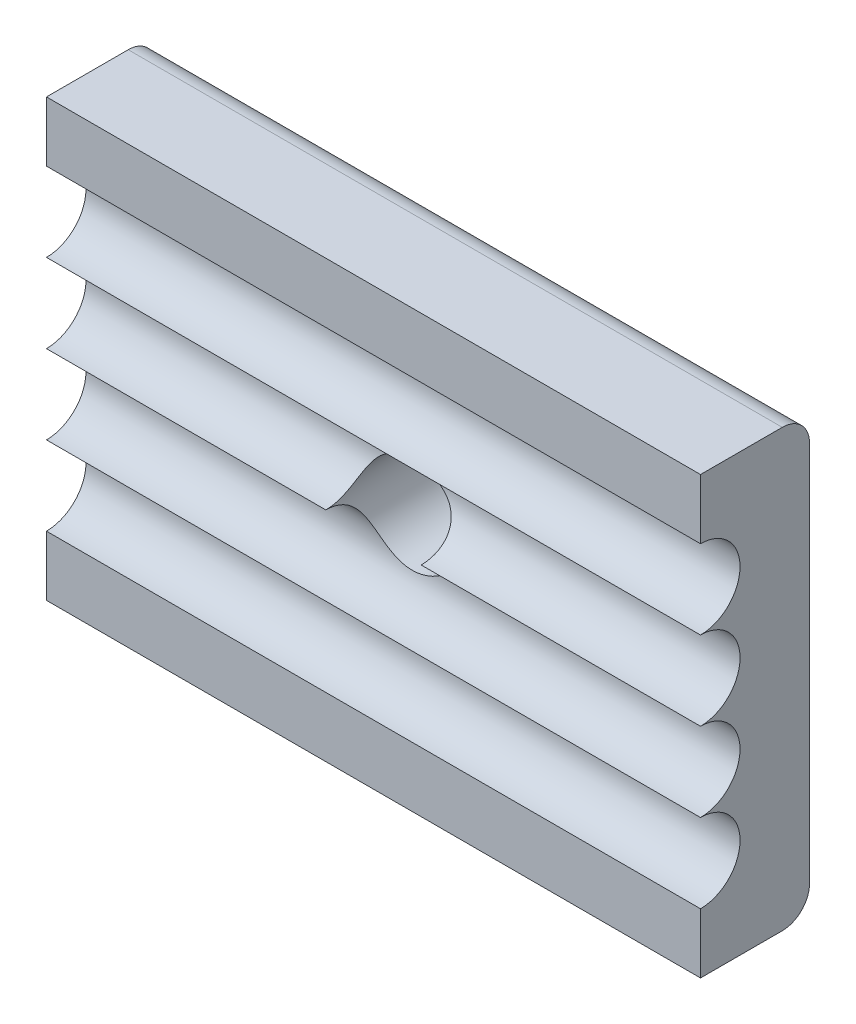
SolidWorks part; units mm, degrees
ref_plane "Front Plane" through (0, 0, 0) normal (0, 0, 1) x (1, 0, 0)
ref_plane "Top Plane" through (0, 0, 0) normal (0, 1, 0) x (1, 0, 0)
ref_plane "Right Plane" through (0, 0, 0) normal (1, 0, 0) x (0, 0, -1)
sketch "Sketch2" plane through (0, 0, 0) normal (0, 0, 1) x (1, 0, 0)
  line L1 (-5.0427, 4) -> (18.9573, 4)
  line L2 (-5.0427, 4) -> (-5.0427, -12)
  line L3 (-5.0427, -12) -> (18.9573, -12)
  line L4 (18.9573, 4) -> (18.9573, -12)
  dimension "D1" = 16
  dimension "D2" = 24
extrude "Boss-Extrude1" add sketch "Sketch2" along normal blind 4
sketch "Sketch3" plane through (0, 0, 4) normal (0, 0, 1) x (1, 0, 0)
  line L0 (-5.0427, 4) -> (-5.0427, -12) construction
  line L1 (18.9573, 4) -> (-5.0427, 4) construction
  circle A0 centre (6.9573, -4) radius 1.75
  point P5 (-5.0427, -4)
  point P8 (6.9573, 4)
  dimension "D1" = 3.5
extrude "Cut-Extrude1" cut sketch "Sketch3" against normal blind 5
sketch "Sketch4" plane through (-5.0427, 0, 0) normal (-1, 0, 0) x (0, 0, 1)
  line L1 (4, 4) -> (4, -12) construction
  line L2 (0, 4) -> (0, -12) construction
  circle A0 centre (4, -5.45) radius 1.45
  circle A1 centre (4, -8.35) radius 1.45
  circle A2 centre (4, -2.55) radius 1.45
  circle A3 centre (4, 0.35) radius 1.45
  point P10 (0, -4)
  point P13 (4, -4.15)
  point P15 (4, -4)
  line M4 (4, -12) -> (4, 4)
  dimension "D1" = 2.9
  dimension "D2" = 2.9
  dimension "D3" = 2.9
  dimension "D4" = 2.9
fillet "Fillet1" radius 1 2 edges at (6.9573, -12, 0) (6.9573, 4, 0)
extrude "Cut-Extrude2" cut sketch "Sketch4" against normal blind 29 contours A1 M4 | A0 M4 | A2 M4 | A3 M4
